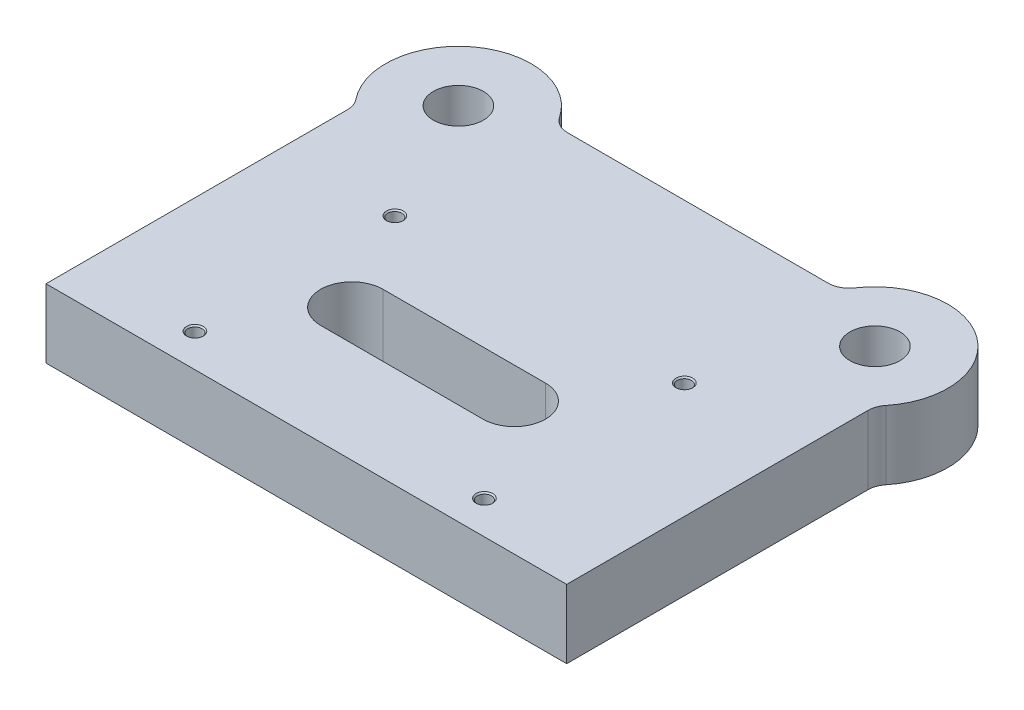
SolidWorks part; units mm, degrees
ref_plane "Front Plane" through (0, 0, 0) normal (0, 0, 1) x (1, 0, 0)
ref_plane "Top Plane" through (0, 0, 0) normal (0, 1, 0) x (1, 0, 0)
ref_plane "Right Plane" through (0, 0, 0) normal (1, 0, 0) x (0, 0, -1)
sketch "Sketch1" plane through (0, 0, 0) normal (0, 1, 0) x (1, 0, 0)
  line L0 (125, 0) -> (-125, 0)
  line L1 (-125, 0) -> (-125, 148.5051)
  line L2 (0, 0) -> (0, 188) construction
  line L3 (68.3772, 188) -> (-68.3772, 188)
  line L4 (125, 0) -> (125, 148.5051)
  arc A0 (-68.3772, 188) -> (-125, 148.5051) centre (-100, 173) ccw
  circle A1 centre (-100, 173) radius 12
  circle A2 centre (100, 173) radius 12
  arc A3 (68.3772, 188) -> (125, 148.5051) centre (100, 173) cw
  dimension "D1" = 70
  dimension "D2" = 24
  dimension "D3" = 173
  dimension "D4" = 188
  dimension "D5" = 250
  dimension "D6" = 200
extrude "Boss-Extrude1" add sketch "Sketch1" along normal blind 33
fillet "Fillet1" radius 10 4 edges at (125, 16.5, -148.5051) (68.3772, 16.5, -188) (-68.3772, 16.5, -188) (-125, 16.5, -148.5051)
hole_wizard "M8 Tapped Hole1" positions "Sketch2" profile "Sketch3" tap size "M8" standard "DIN" end condition up to next
sketch "Sketch2" plane through (0, 33, 0) normal (0, 1, 0) x (1, 0, 0)
  point P0 (-69.5, 112)
  point P3 (69.5, 112)
  point P6 (69.5, 16)
  point P9 (-69.5, 16)
sketch "Sketch3" plane through (-69.5, 33, -112) normal (1, 0, 0) x (0, 0, 1)
  line L0 (0, 0) -> (0, 33)
  line L1 (0, 33) -> (3.4, 33)
  line L2 (3.4, 33) -> (3.4, 0.625)
  line L3 (3.4, 0.625) -> (4.025, 0)
  line L5 (4.025, 0) -> (0, 0)
  line L6 (-3.4, 0.625) -> (-4.025, 0) construction
  line L11 (0, -6.35) -> (0, 107.95) construction
  dimension "Thru Tap Drill Dia." = 6.8
  dimension "Thru Tap Drill Depth" = 33
  dimension "Near C'Sink Dia." = 8.05
  dimension "Near C'Sink Angle" = 90
cosmetic thread "Hole Thread1" parameters "D2"=8
cosmetic thread "Hole Thread2" parameters "D2"=8
cosmetic thread "Hole Thread3" parameters "D2"=8
cosmetic thread "Hole Thread4" parameters "D2"=8
sketch "Sketch4" plane through (0, 33, 0) normal (0, 1, 0) x (1, 0, 0)
  line L0 (-41.7731, 63.6024) -> (36.2269, 63.6024) construction
  line L1 (-41.7731, 78.6024) -> (36.2269, 78.6024)
  line L2 (-41.7731, 48.6024) -> (36.2269, 48.6024)
  arc A0 (-41.7731, 78.6024) -> (-41.7731, 48.6024) centre (-41.7731, 63.6024) ccw
  arc A1 (36.2269, 48.6024) -> (36.2269, 78.6024) centre (36.2269, 63.6024) ccw
  point P2 (-2.7731, 63.6024)
  dimension "D2" = 15
  dimension "D1" = 78
extrude "Cut-Extrude1" cut sketch "Sketch4" against normal up to next
